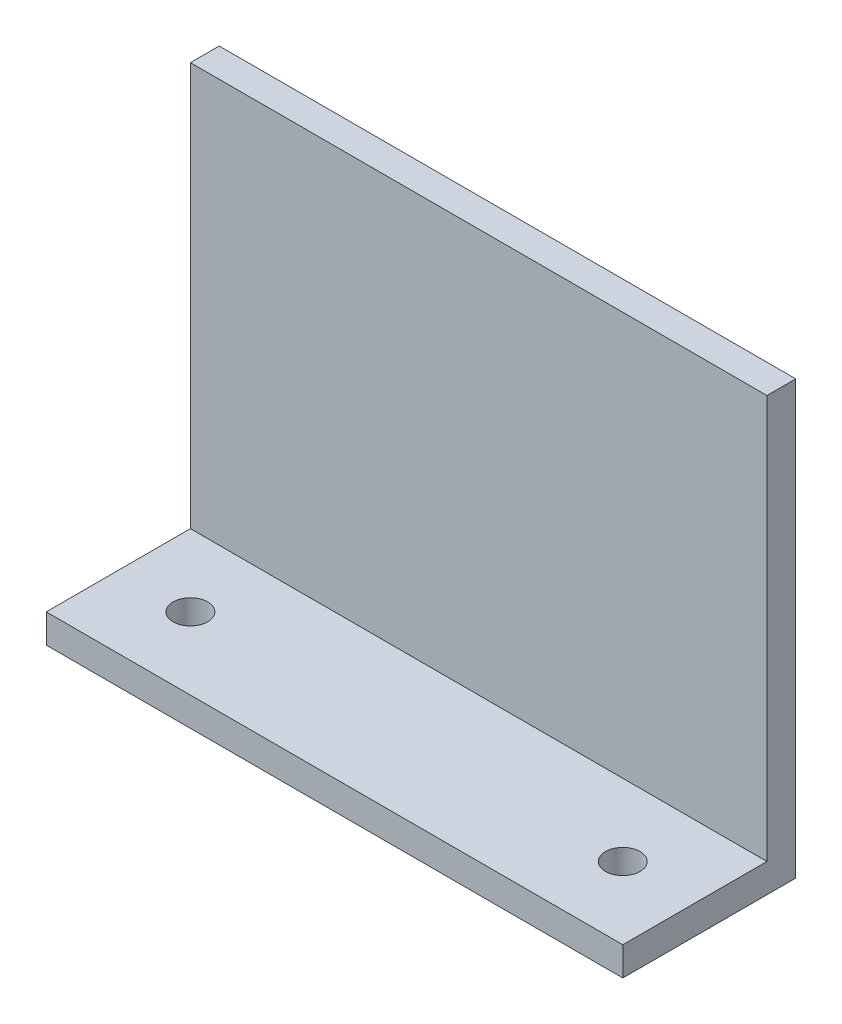
SolidWorks part; units mm, degrees
ref_plane "Płaszczyzna przednia" through (0, 0, 0) normal (0, 0, 1) x (1, 0, 0)
ref_plane "Płaszczyzna górna" through (0, 0, 0) normal (0, 1, 0) x (1, 0, 0)
ref_plane "Płaszczyzna prawa" through (0, 0, 0) normal (1, 0, 0) x (0, 0, -1)
sketch "Szkic1" plane through (0, 0, 0) normal (0, 0, 1) x (1, 0, 0)
  line L1 (-100, -75) -> (100, -75)
  line L2 (-100, -75) -> (-100, 75)
  line L3 (-100, 75) -> (100, 75)
  line L4 (100, -75) -> (100, 75)
  line L5 (-100, -75) -> (100, 75) construction
  line L6 (-100, 75) -> (100, -75) construction
  point P0 (0, 0)
  dimension "D1" = 200
  dimension "D2" = 150
extrude "Dodanie-wyciągnięcie1" add sketch "Szkic1" along normal blind 10
sketch "Szkic2" plane through (0, 0, 10) normal (0, 0, 1) x (1, 0, 0)
  line L0 (100, -75) -> (100, 75) construction
  line L1 (-100, -75) -> (100, -75)
  line L2 (-100, -75) -> (-100, -65)
  line L3 (-100, -65) -> (100, -65)
  line L4 (100, -75) -> (100, -65)
  dimension "D1" = 10
extrude "Dodanie-wyciągnięcie2" add sketch "Szkic2" along normal blind 50
hole_wizard "Otwór pod śrubę M101" positions "Szkic3" profile "Szkic4" hole size "M10" standard "Ansi Metric" end condition through all
sketch "Szkic3" plane through (0, -65, 0) normal (0, 1, 0) x (1, 0, 0)
  line L0 (100, -60) -> (-100, -60) construction
  line L1 (-100, -60) -> (-100, -10) construction
  point P0 (-75, -35)
  dimension "D1" = 25
  dimension "D2" = 25
sketch "Szkic4" plane through (-75, -65, 35) normal (1, 0, 0) x (0, 0, 1)
  line L0 (0, 0) -> (0, 10)
  line L1 (0, 10) -> (6, 10)
  line L2 (6, 10) -> (6, 0)
  line L5 (6, 0) -> (0, 0)
  line L11 (0, -6.35) -> (0, 107.95) construction
  dimension "Średnica otworu na wylot" = 12
  dimension "Głębokość otworu na wylot" = 10
pattern_linear "Szyk liniowy2" count 2 spacing 150 along (1, 0, 0) of "Otwór pod śrubę M101"
